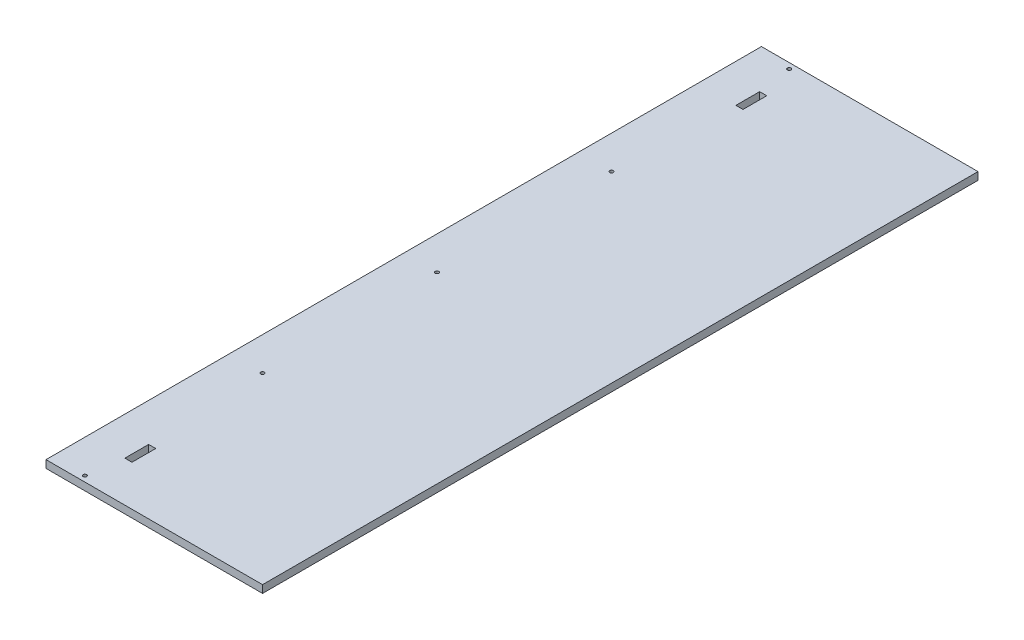
SolidWorks part; units mm, degrees
ref_plane "Front Plane" through (0, 0, 0) normal (0, 0, 1) x (1, 0, 0)
ref_plane "Top Plane" through (0, 0, 0) normal (0, 1, 0) x (1, 0, 0)
ref_plane "Right Plane" through (0, 0, 0) normal (1, 0, 0) x (0, 0, -1)
sketch "Sketch1" plane through (0, 0, 0) normal (0, 1, 0) x (1, 0, 0)
  line L1 (-50, 609.6) -> (50, 609.6)
  line L2 (-50, 609.6) -> (-50, -609.6)
  line L3 (-50, -609.6) -> (50, -609.6)
  line L4 (50, 609.6) -> (50, -609.6)
  line L5 (-50, 609.6) -> (50, -609.6) construction
  line L6 (-50, -609.6) -> (50, 609.6) construction
  point P0 (0, 0)
  dimension "D1" = 1219.2
  dimension "D2" = 100
extrude "Boss-Extrude1" add sketch "Sketch1" along normal blind 13
sketch "Sketch3" plane through (0, 13, 0) normal (0, 1, 0) x (1, 0, 0)
  line L0 (6.743, -596.315) -> (6.743, -604.8608) construction
sketch "Sketch4" plane through (0, 13, 0) normal (0, 1, 0) x (1, 0, 0)
  line L0 (6.743, -596.315) -> (6.743, -604.8608) construction
  line L1 (-50, -609.6) -> (50, -609.6) construction
  line L3 (50, 609.6) -> (-50, 609.6) construction
  line L4 (50, -609.6) -> (50, 609.6) construction
  circle A0 centre (6.743, -600.1) radius 3
  circle A1 centre (6.743, -297.3) radius 3
  circle A2 centre (6.743, 0) radius 3
  circle A3 centre (6.743, 297.3) radius 3
  circle A4 centre (6.743, 600.1) radius 3
  dimension "D1" = 6
  dimension "D4" = 9.5
  dimension "D3" = 43.257
  dimension "D5" = 6
  dimension "D6" = 297.3
  dimension "D7" = 6
  dimension "D8" = 6
  dimension "D10" = 297.3
  dimension "D11" = 6
  dimension "D2" = 9.5
extrude "Cut-Extrude1" cut sketch "Sketch4" against normal blind 20
sketch "Sketch5" plane through (0, 0, 609.6) normal (0, 0, 1) x (1, 0, 0)
  line L5 (-50, 13) -> (50, 13) construction
  line L6 (39.2642, 13) -> (319, 13)
  line L7 (39.2642, 13) -> (39.2642, 0)
  line L8 (39.2642, 0) -> (319, 0)
  line L9 (319, 13) -> (319, 0)
  line L10 (50, 13) -> (50, 0) construction
  line L11 (-50, 0) -> (50, 0) construction
  dimension "D2" = 269
extrude "Boss-Extrude2" add sketch "Sketch5" against normal up to surface (1219.2 mm away) up to face at (0, 6.5, -609.6)
sketch "Sketch6" plane through (0, 13, 0) normal (0, 1, 0) x (1, 0, 0)
  line L0 (-50, 609.6) -> (-50, -609.6) construction
  line L4 (15, -499.72) -> (27.1, -499.72)
  line L5 (15, -499.72) -> (15, -540.22)
  line L6 (15, -540.22) -> (27.1, -540.22)
  line L7 (27.1, -499.72) -> (27.1, -540.22)
  line L8 (-50, -609.6) -> (319, -609.6) construction
  line L9 (15, 541.53) -> (27.1, 541.53)
  line L10 (15, 541.53) -> (15, 501.03)
  line L11 (15, 501.03) -> (27.1, 501.03)
  line L12 (27.1, 541.53) -> (27.1, 501.03)
  dimension "D1" = 40.5
  dimension "D2" = 12.1
  dimension "D3" = 65
  dimension "D4" = 69.38
  dimension "D6" = 1041.25
  dimension "D5" = 2
extrude "Cut-Extrude2" cut sketch "Sketch6" against normal blind 20
